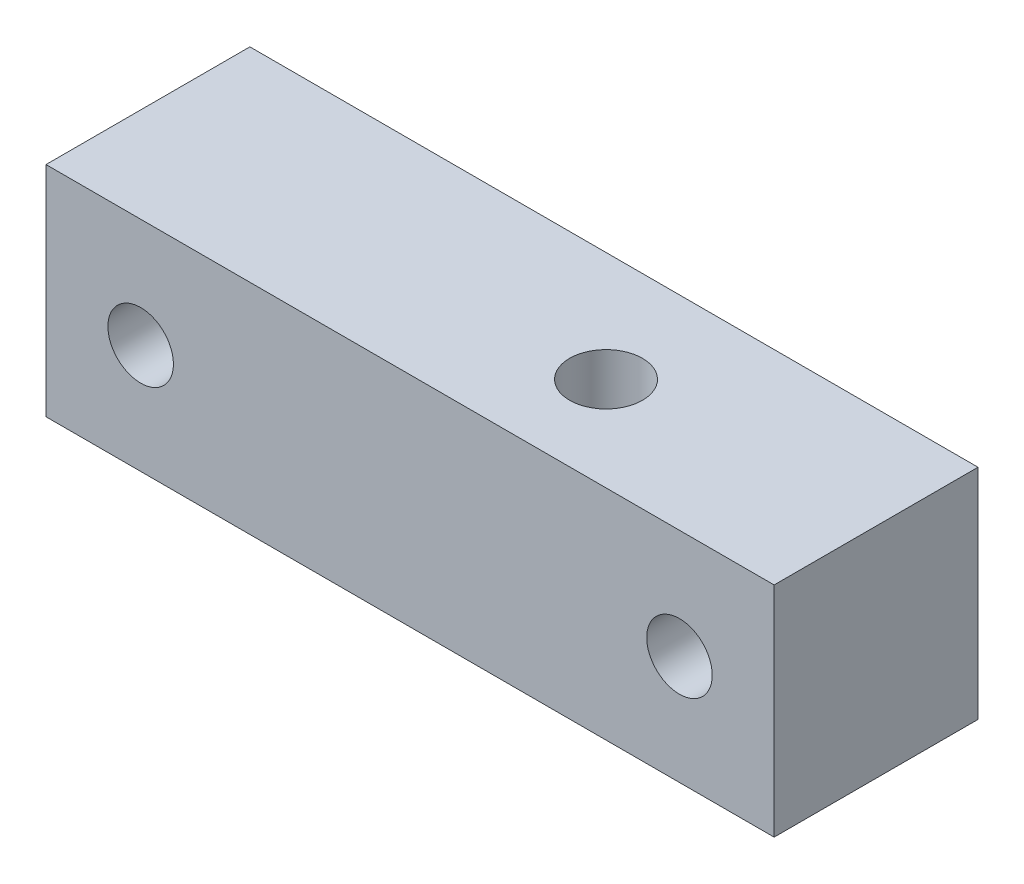
SolidWorks part; units mm, degrees
material "Plain Carbon Steel"
ref_plane "Front Plane" through (0, 0, 0) normal (0, 0, 1) x (1, 0, 0)
ref_plane "Top Plane" through (0, 0, 0) normal (0, 1, 0) x (1, 0, 0)
ref_plane "Right Plane" through (0, 0, 0) normal (1, 0, 0) x (0, 0, -1)
sketch "Sketch1" plane through (0, 0, 0) normal (0, 0, 1) x (1, 0, 0)
  line L0 (0, 0) -> (50, 0)
  line L1 (50, 0) -> (50, 15)
  line L2 (50, 15) -> (0, 15)
  line L3 (0, 15) -> (0, 0)
  dimension "D1" = 15
  dimension "D2" = 50
extrude "Boss-Extrude1" add sketch "Sketch1" along normal blind 14
sketch "Sketch2" plane through (0, 15, 0) normal (0, 1, 0) x (1, 0, 0)
  line L0 (-8.4278, -7.542) -> (50.4091, -7.542) construction
  line L1 (50, -14) -> (50, 0) construction
  circle A0 centre (32, -7.542) radius 2.5
  dimension "D2" = 5
  dimension "D1" = 18
extrude "Cut-Extrude1" cut sketch "Sketch2" against normal through all
sketch "Sketch3" plane through (0, 0, 14) normal (0, 0, 1) x (1, 0, 0)
  line L0 (0, 7.5) -> (-4.1873, 7.5) construction
  line L1 (0, 15) -> (0, 0) construction
  line L2 (-4.1873, 7.5) -> (53.216, 7.5) construction
  line L3 (25, 15) -> (25, 16.7829) construction
  line L4 (50, 15) -> (0, 15) construction
  line L5 (25, 16.7829) -> (25, -2.9601) construction
  circle A0 centre (6.5, 7.5) radius 2.25
  circle A1 centre (43.5, 7.5) radius 2.25
  dimension "D1" = 4.5
  dimension "D2" = 4.5
  dimension "D3" = 18.5
  dimension "D4" = 18.5
extrude "Cut-Extrude2" cut sketch "Sketch3" against normal through all
